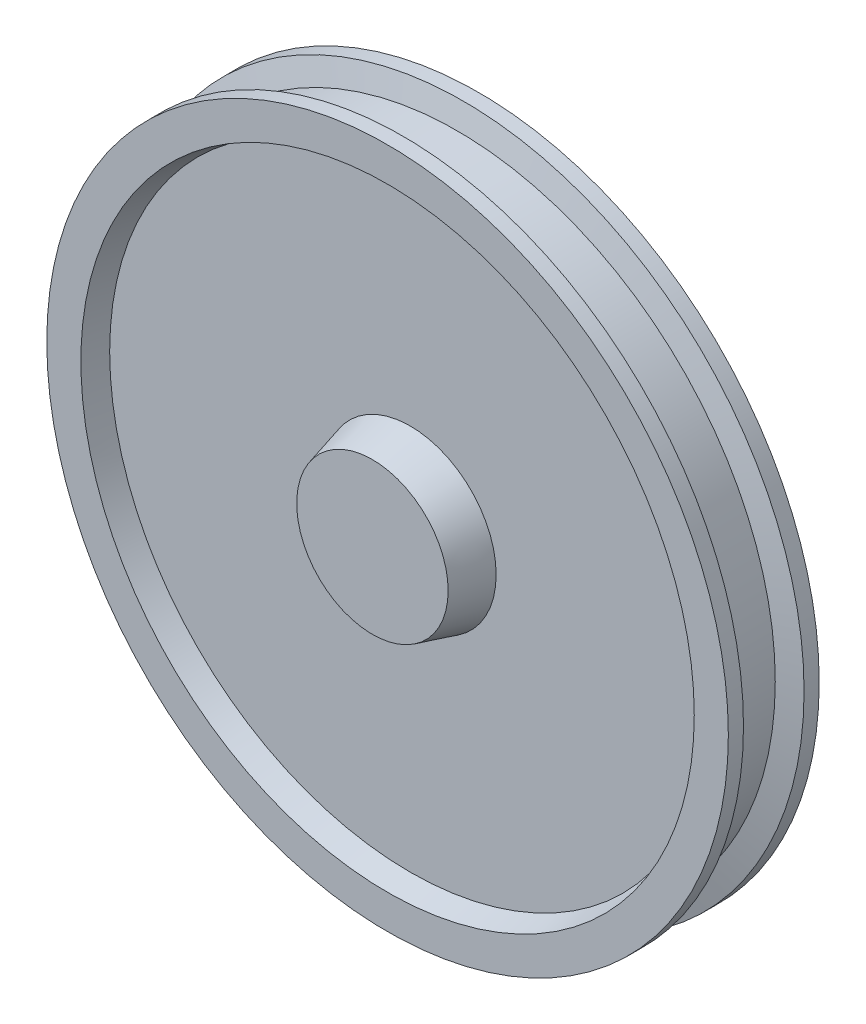
SolidWorks part; units mm, degrees
material "1060 Alloy"
ref_plane "Front Plane" through (0, 0, 0) normal (0, 0, 1) x (1, 0, 0)
ref_plane "Top Plane" through (0, 0, 0) normal (0, 1, 0) x (1, 0, 0)
ref_plane "Right Plane" through (0, 0, 0) normal (1, 0, 0) x (0, 0, -1)
sketch "Sketch1" plane through (0, 0, 0) normal (1, 0, 0) x (0, 0, -1)
  line L0 (-80, 0) -> (80, 0) construction
  line L1 (-80, 0) -> (-80, 100)
  line L2 (-80, 100) -> (-30, 113.3975)
  line L3 (-30, 113.3975) -> (-30, 396.9615)
  line L4 (-30, 396.9615) -> (-60, 405)
  line L5 (-60, 405) -> (-60, 450)
  line L6 (-60, 450) -> (-40, 450)
  line L7 (0, 0) -> (0, 563.296) construction
  line L8 (-40, 450) -> (-31.9615, 420)
  line L9 (-31.9615, 420) -> (31.9615, 420)
  line L10 (-80, 0) -> (80, 0)
  line L11 (80, 0) -> (80, 100)
  line L12 (80, 100) -> (30, 113.3975)
  line L13 (30, 113.3975) -> (30, 396.9615)
  line L14 (30, 396.9615) -> (60, 405)
  line L15 (60, 405) -> (60, 450)
  line L16 (60, 450) -> (40, 450)
  line L17 (40, 450) -> (31.9615, 420)
  point P3 (-63.6069, 444.241)
  point P4 (0, 0)
  point P8 (-10.5862, 373.0495)
  point P15 (-5.2816, 398.4864)
  point P16 (-24.3964, 396.3697)
  point P17 (-44.6855, 444.7868)
  point P25 (0, 420)
  dimension "D3" = 15
  dimension "D4" = 100
  dimension "D2" = 450
  dimension "D5" = 30
  dimension "D6" = 120
  dimension "D7" = 20
  dimension "D8" = 15
  dimension "D9" = 15
  dimension "D10" = 60
  dimension "D11" = 45
  dimension "D12" = 160
revolve "Revolve1" add sketch "Sketch1" angle 360 about L10
equation "\"A\"= 120"
equation "\"B\"= 900"
equation "\"D2@Sketch1\"=\"B\"/2"
equation "\"D6@Sketch1\"=\"A\""
equation "\"D12@Sketch1\"=\"A\"+40"
